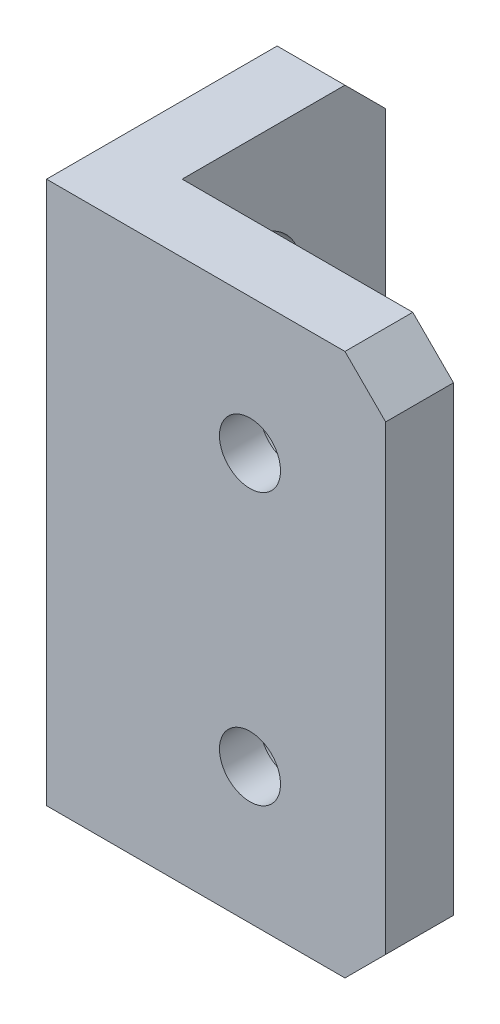
SolidWorks part; units mm, degrees
ref_plane "Front Plane" through (0, 0, 0) normal (0, 0, 1) x (1, 0, 0)
ref_plane "Top Plane" through (0, 0, 0) normal (0, 1, 0) x (1, 0, 0)
ref_plane "Right Plane" through (0, 0, 0) normal (1, 0, 0) x (0, 0, -1)
sketch "Sketch1" plane through (0, 0, 0) normal (0, 1, 0) x (1, 0, 0)
  line L1 (0, 0) -> (25, 0)
  line L3 (5, 5) -> (25, 5)
  line L4 (25, 0) -> (25, 5)
  line L6 (0, 0) -> (0, 20)
  line L7 (0, 20) -> (5, 20)
  line L8 (5, 5) -> (5, 20)
  point P9 (0, 0)
  point P10 (-2.8399, 0)
  point P11 (0, -1.8897)
  dimension "D1" = 5
  dimension "D2" = 25
  dimension "D3" = 5
  dimension "D4" = 20
extrude "Boss-Extrude1" add sketch "Sketch1" along normal blind 40
sketch "Sketch2" plane through (0, 0, 0) normal (-1, 0, 0) x (0, 0, 1)
  line L0 (-10, 0) -> (-10, 40) construction
  line L1 (-20, 0) -> (0, 0) construction
  line L2 (-20, 40) -> (0, 40) construction
  line L3 (-20, 20) -> (0, 20) construction
  line L4 (-20, 40) -> (-20, 0) construction
  line L5 (0, 40) -> (0, 0) construction
  circle A0 centre (-10, 10) radius 2.25
  circle A1 centre (-10, 30) radius 2.25
  dimension "D1" = 10
  dimension "D2" = 4.5
extrude "Cut-Extrude1" cut sketch "Sketch2" against normal up to next
sketch "Sketch3" plane through (0, 0, -5) normal (0, 0, -1) x (-1, 0, 0)
  line L0 (-15, 0) -> (-15, 40) construction
  line L1 (-25, 0) -> (-5, 0) construction
  line L2 (-25, 40) -> (-5, 40) construction
  line L3 (-25, 20) -> (-5, 20) construction
  line L4 (-25, 40) -> (-25, 0) construction
  line L5 (-5, 40) -> (-5, 0) construction
  circle A0 centre (-15, 10) radius 2.25
  circle A1 centre (-15, 30) radius 2.25
  dimension "D1" = 10
  dimension "D2" = 4.5
extrude "Cut-Extrude2" cut sketch "Sketch3" against normal up to next
sketch "Sketch4" plane through (0, 0, -5) normal (0, 0, -1) x (-1, 0, 0)
  line L0 (-25, 20) -> (-5, 20) construction
  line L1 (-25, 40) -> (-25, 0) construction
  line L2 (-5, 40) -> (-5, 0) construction
  circle A0 centre (-15, 10) radius 3.75
  circle A1 centre (-15, 30) radius 3.75
  dimension "D1" = 7.5
extrude "Cut-Extrude3" cut sketch "Sketch4" against normal blind 2
sketch "Sketch5" plane through (5, 0, 0) normal (1, 0, 0) x (0, 0, -1)
  line L0 (20, 20) -> (5, 20) construction
  line L1 (20, 40) -> (20, 0) construction
  line L2 (5, 40) -> (5, 0) construction
  circle A0 centre (10, 30) radius 3.75
  circle A1 centre (10, 10) radius 3.75
  dimension "D1" = 7.5
extrude "Cut-Extrude4" cut sketch "Sketch5" against normal blind 2
chamfer "Chamfer1" distance 3 angle 45 4 edges at (2.5, 40, -20) (25, 40, -2.5) (25, 0, -2.5) (2.5, 0, -20)
